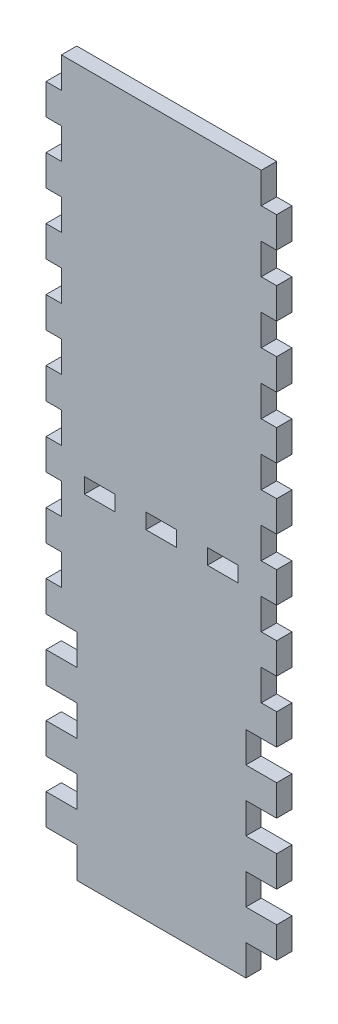
SolidWorks part; units mm, degrees
material "Pine"
ref_plane "Front Plane" through (0, 0, 0) normal (0, 0, 1) x (1, 0, 0)
ref_plane "Top Plane" through (0, 0, 0) normal (0, 1, 0) x (1, 0, 0)
ref_plane "Right Plane" through (0, 0, 0) normal (1, 0, 0) x (0, 0, -1)
sketch "Sketch1" plane through (0, 0, 0) normal (0, 0, 1) x (1, 0, 0)
  line L1 (0, 0) -> (95.25, 0)
  line L2 (0, 0) -> (0, 292.1)
  line L3 (0, 292.1) -> (95.25, 292.1)
  line L4 (95.25, 0) -> (95.25, 292.1)
  dimension "D1" = 95.25
  dimension "D2" = 292.1
extrude "Boss-Extrude1" add sketch "Sketch1" along normal blind 6.35
sketch "Sketch2" plane through (0, 0, 6.35) normal (0, 0, 1) x (1, 0, 0)
  line L0 (0, 292.1) -> (0, 0) construction
  line L1 (0, 0) -> (6.35, 0)
  line L2 (0, 0) -> (0, 12.7)
  line L3 (0, 12.7) -> (6.35, 12.7)
  line L4 (6.35, 0) -> (6.35, 12.7)
  line L5 (95.25, 0) -> (95.25, 292.1) construction
  line L6 (95.25, 0) -> (88.9, 0)
  line L7 (95.25, 0) -> (95.25, 12.7)
  line L8 (95.25, 12.7) -> (88.9, 12.7)
  line L9 (88.9, 0) -> (88.9, 12.7)
  dimension "D2" = 12.7
  dimension "D3" = 6.35
extrude "Cut-Extrude1" cut sketch "Sketch2" against normal through all
pattern_linear "LPattern1" count 12 spacing 25.4 along (0, 1, 0) of "Cut-Extrude1"
sketch "Sketch3" plane through (0, 0, 6.35) normal (0, 0, 1) x (1, 0, 0)
  line L0 (6.35, 0) -> (88.9, 0) construction
  line L1 (88.9, 12.7) -> (82.55, 12.7)
  line L2 (88.9, 12.7) -> (88.9, 0)
  line L3 (88.9, 0) -> (82.55, 0)
  line L4 (82.55, 12.7) -> (82.55, 0)
  line L5 (95.25, 12.7) -> (88.9, 12.7) construction
  line L6 (6.35, 12.7) -> (12.7, 12.7)
  line L7 (6.35, 12.7) -> (6.35, 0)
  line L8 (6.35, 0) -> (12.7, 0)
  line L9 (12.7, 12.7) -> (12.7, 0)
extrude "Cut-Extrude2" cut sketch "Sketch3" against normal through all
pattern_linear "LPattern2" count 4 spacing 25.4 along (0, 1, 0) of "Cut-Extrude2"
sketch "Sketch4" plane through (0, 0, 6.35) normal (0, 0, 1) x (1, 0, 0)
  line L0 (6.35, 139.7) -> (0, 139.7) construction
  line L1 (41.275, 146.05) -> (53.975, 146.05)
  line L2 (41.275, 146.05) -> (41.275, 139.7)
  line L3 (41.275, 139.7) -> (53.975, 139.7)
  line L4 (53.975, 146.05) -> (53.975, 139.7)
  line L5 (47.625, 139.7) -> (47.625, 0) construction
  line L6 (12.7, 0) -> (82.55, 0) construction
  dimension "D1" = 6.35
  dimension "D2" = 12.7
extrude "Cut-Extrude3" cut sketch "Sketch4" against normal through all
pattern_linear "LPattern3" count 2 spacing 25.4 along (-1, 0, 0) count 2 spacing 25.4 along (1, 0, 0) of "Cut-Extrude3"
